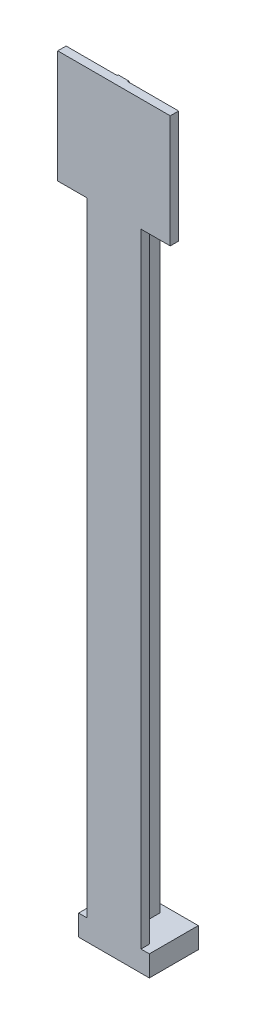
SolidWorks part; units mm, degrees
ref_plane "Front Plane" through (0, 0, 0) normal (0, 0, 1) x (1, 0, 0)
ref_plane "Top Plane" through (0, 0, 0) normal (0, 1, 0) x (1, 0, 0)
ref_plane "Right Plane" through (0, 0, 0) normal (1, 0, 0) x (0, 0, -1)
sketch "Sketch1" plane through (0, 0, 0) normal (0, 1, 0) x (1, 0, 0)
  line L1 (0, 0) -> (16.9, 0)
  line L2 (0, 0) -> (0, 11.7)
  line L3 (0, 11.7) -> (16.9, 11.7)
  line L4 (16.9, 0) -> (16.9, 11.7)
  dimension "D1" = 16.9
  dimension "D2" = 11.7
extrude "Boss-Extrude1" add sketch "Sketch1" along normal blind 5
sketch "Sketch2" plane through (0, 0, 0) normal (0, -1, 0) x (1, 0, 0)
  line L0 (0, -5.85) -> (16.9, -5.85) construction
  line L1 (2.925, -2.925) -> (13.975, -2.925)
  line L2 (2.925, -2.925) -> (2.925, -8.775)
  line L3 (2.925, -8.775) -> (13.975, -8.775)
  line L4 (13.975, -2.925) -> (13.975, -8.775)
  line L5 (0, -11.7) -> (0, 0) construction
  line L6 (16.9, 0) -> (16.9, -11.7) construction
  line L7 (8.45, 0) -> (8.45, -11.7) construction
  line L8 (0, 0) -> (16.9, 0) construction
  line L9 (16.9, -11.7) -> (0, -11.7) construction
  dimension "D1" = 11.05
  dimension "D2" = 5.85
extrude "Cut-Extrude1" cut sketch "Sketch2" against normal blind 0.95
sketch "Sketch3" plane through (0, 0.95, 0) normal (0, -1, 0) x (1, 0, 0)
  line L0 (13.975, -2.925) -> (2.925, -2.925) construction
  line L1 (3.375, -3.325) -> (13.575, -3.325)
  line L2 (3.375, -3.325) -> (3.375, -8.425)
  line L3 (3.375, -8.425) -> (13.575, -8.425)
  line L4 (13.575, -3.325) -> (13.575, -8.425)
  line L5 (13.975, -8.775) -> (13.975, -2.925) construction
  dimension "D1" = 10.2
  dimension "D2" = 5.1
  dimension "D3" = 0.4
  dimension "D4" = 0.4
extrude "Cut-Extrude2" cut sketch "Sketch3" against normal blind 3
sketch "Sketch4" plane through (0, 0.95, 0) normal (0, -1, 0) x (1, 0, 0)
  line L1 (3.375, -3.325) -> (13.575, -3.325)
  line L2 (3.375, -3.325) -> (3.375, -8.425)
  line L3 (3.375, -8.425) -> (13.575, -8.425)
  line L4 (13.575, -3.325) -> (13.575, -8.425)
extrude "Boss-Extrude2" add sketch "Sketch4" against normal blind 1
sketch "Sketch5" plane through (0, 5, 0) normal (0, 1, 0) x (1, 0, 0)
  line L0 (0, 0) -> (16.9, 0) construction
  line L1 (2, 0) -> (2, 2)
  line L2 (2, 2) -> (7.2, 2)
  line L3 (7.2, 2) -> (7.2, 9.7)
  line L4 (7.2, 9.7) -> (9.7, 9.7)
  line L5 (9.7, 9.7) -> (9.7, 2)
  line L6 (9.7, 2) -> (14.9, 2)
  line L7 (14.9, 2) -> (14.9, 0)
  line L8 (0, 11.7) -> (0, 0) construction
  line L9 (16.9, 0) -> (16.9, 11.7) construction
  line L10 (16.9, 11.7) -> (0, 11.7) construction
  line L15 (0, 11.7) -> (0, 0)
  line L16 (0, 0) -> (16.9, 0)
  line L17 (16.9, 0) -> (16.9, 11.7)
  line L18 (16.9, 11.7) -> (0, 11.7)
  line L20 (2, 0) -> (14.9, 0)
  dimension "D1" = 2
  dimension "D2" = 2
  dimension "D3" = 2
  dimension "D4" = 5.2
  dimension "D5" = 5.2
  dimension "D6" = 2
  dimension "D7" = 0
extrude "Boss-Extrude3" add sketch "Sketch5" along normal blind 176
sketch "Sketch6" plane through (0, 0, 0) normal (0, 0, 1) x (1, 0, 0)
  line L0 (14.9, 181) -> (14.9, 5) construction
  line L1 (-5, 181) -> (21.9, 181)
  line L2 (-5, 181) -> (-5, 154.05)
  line L3 (-5, 154.05) -> (21.9, 154.05)
  line L4 (21.9, 181) -> (21.9, 154.05)
  line L5 (2, 181) -> (2, 5) construction
  line L6 (2, 181) -> (14.9, 181) construction
  dimension "D1" = 7
  dimension "D2" = 7
  dimension "D3" = 26.95
extrude "Boss-Extrude4" add sketch "Sketch6" against normal blind 2
chamfer "Chamfer1" distance 14 angle 28 1 edges at (8.45, 181, -9.7)
